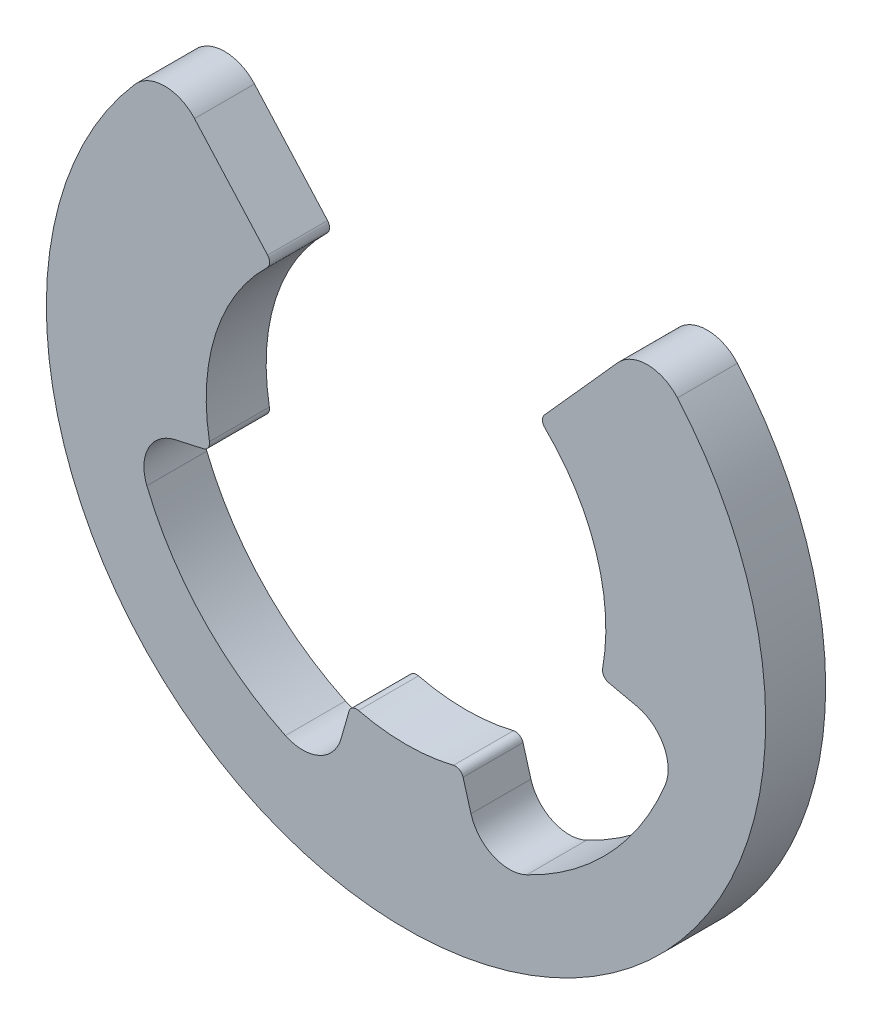
SolidWorks part; units mm, degrees
ref_plane "Piano frontale" through (0, 0, 0) normal (0, 0, 1) x (1, 0, 0)
ref_plane "Piano superiore" through (0, 0, 0) normal (0, 1, 0) x (1, 0, 0)
ref_plane "Piano destro" through (0, 0, 0) normal (1, 0, 0) x (0, 0, -1)
sketch "Schizzo1" plane through (0, 0, 0) normal (0, 0, 1) x (1, 0, 0)
  line L3 (0.7137, -2.4981) -> (0.8126, -2.8442)
  line L4 (-0.7137, -2.4981) -> (-0.8126, -2.8442)
  line L9 (-2.8876, -0.6417) -> (-2.5362, -0.5636)
  line L10 (2.8876, -0.6417) -> (2.5362, -0.5636)
  line L11 (-2.6458, 2.958) -> (-1.7321, 1.9365)
  line L12 (2.6458, 2.958) -> (1.7321, 1.9365)
  arc A3 (-3.3957, 2.9528) -> (3.3957, 2.9528) centre (0, 0) ccw
  arc A4 (1.509, -3.158) -> (3.2423, -1.3181) centre (0, 0) ccw
  arc A6 (-0.5938, -2.4284) -> (0.5938, -2.4284) centre (0, 0) ccw
  arc A7 (2.4595, -0.4481) -> (1.7371, 1.7979) centre (0, 0) ccw
  arc A9 (-3.2423, -1.3181) -> (-1.509, -3.158) centre (0, 0) ccw
  arc A10 (-1.7371, 1.7979) -> (-2.4595, -0.4481) centre (0, 0) ccw
  arc A11 (2.6458, 2.958) -> (3.3957, 2.9528) centre (3.0184, 2.6247) cw
  arc A12 (-3.3957, 2.9528) -> (-2.6458, 2.958) centre (-3.0184, 2.6247) cw
  arc A13 (-3.2423, -1.3181) -> (-2.8876, -0.6417) centre (-2.7791, -1.1298) cw
  arc A14 (3.2423, -1.3181) -> (2.8876, -0.6417) centre (2.7791, -1.1298) ccw
  arc A15 (1.509, -3.158) -> (0.8126, -2.8442) centre (1.2934, -2.7069) cw
  arc A16 (-1.509, -3.158) -> (-0.8126, -2.8442) centre (-1.2934, -2.7069) ccw
  arc A17 (1.7371, 1.7979) -> (1.7321, 1.9365) centre (1.8066, 1.8698) cw
  arc A18 (-1.7371, 1.7979) -> (-1.7321, 1.9365) centre (-1.8066, 1.8698) ccw
  arc A19 (2.4595, -0.4481) -> (2.5362, -0.5636) centre (2.5579, -0.466) ccw
  arc A20 (-2.5362, -0.5636) -> (-2.4595, -0.4481) centre (-2.5579, -0.466) ccw
  arc A21 (0.5938, -2.4284) -> (0.7137, -2.4981) centre (0.6176, -2.5256) cw
  arc A22 (-0.5938, -2.4284) -> (-0.7137, -2.4981) centre (-0.6176, -2.5256) ccw
  point P29 (-1.6667, 1.8634)
  dimension "D1" = 0.5
  dimension "D2" = 0.1
  dimension "D3" = 0.1
  dimension "D4" = 0.1
extrude "Estrusione-Estrusione1" add sketch "Schizzo1" along normal blind 0.75
